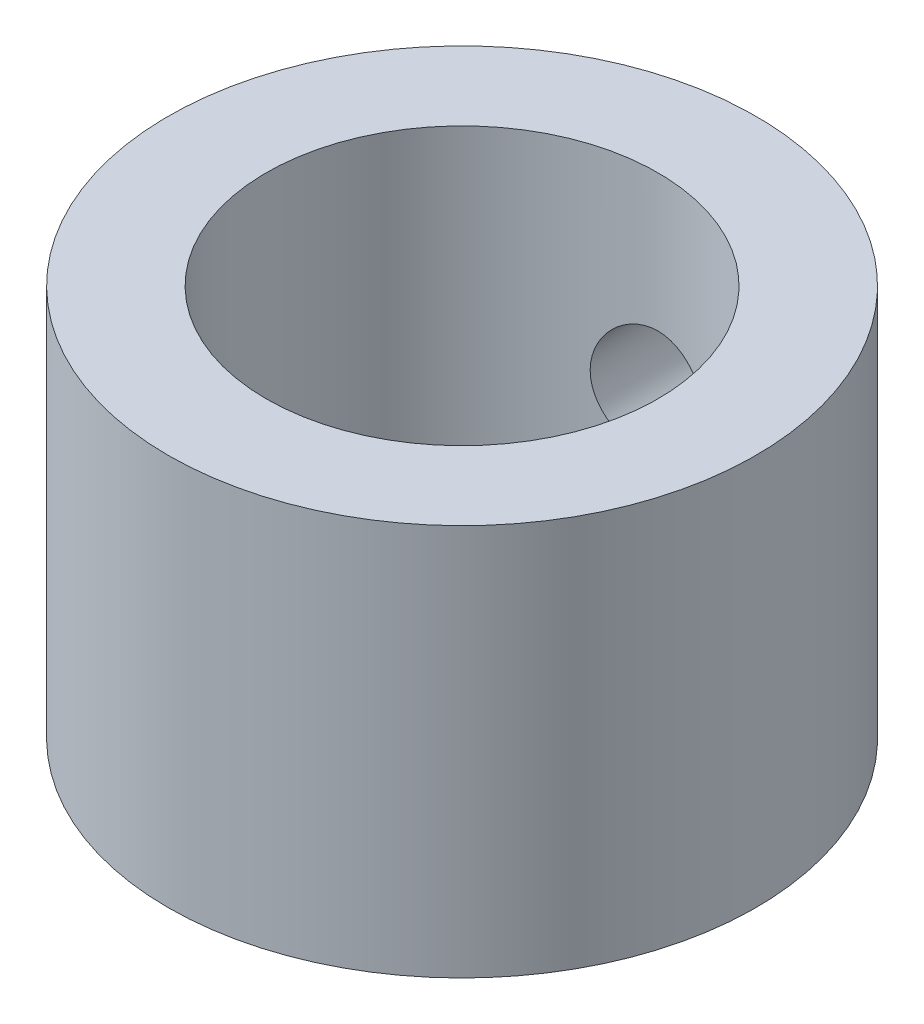
SolidWorks part; units mm, degrees
ref_plane "Front Plane" through (0, 0, 0) normal (0, 0, 1) x (1, 0, 0)
ref_plane "Top Plane" through (0, 0, 0) normal (0, 1, 0) x (1, 0, 0)
ref_plane "Right Plane" through (0, 0, 0) normal (1, 0, 0) x (0, 0, -1)
sketch "Sketch1" plane through (0, 0, 0) normal (0, 1, 0) x (1, 0, 0)
  circle A0 centre (0, 0) radius 7.5
  circle A1 centre (0, 0) radius 5
  dimension "D1" = 10
  dimension "D2" = 15
extrude "Boss-Extrude1" add sketch "Sketch1" along normal mid plane 10
sketch "Sketch5" plane through (0, 0, 0) normal (0, 0, 1) x (1, 0, 0)
  circle A0 centre (0, 0) radius 1.5
  dimension "D1" = 3
extrude "Cut-Extrude1" cut sketch "Sketch5" against normal up to surface (7.3485 mm away)
